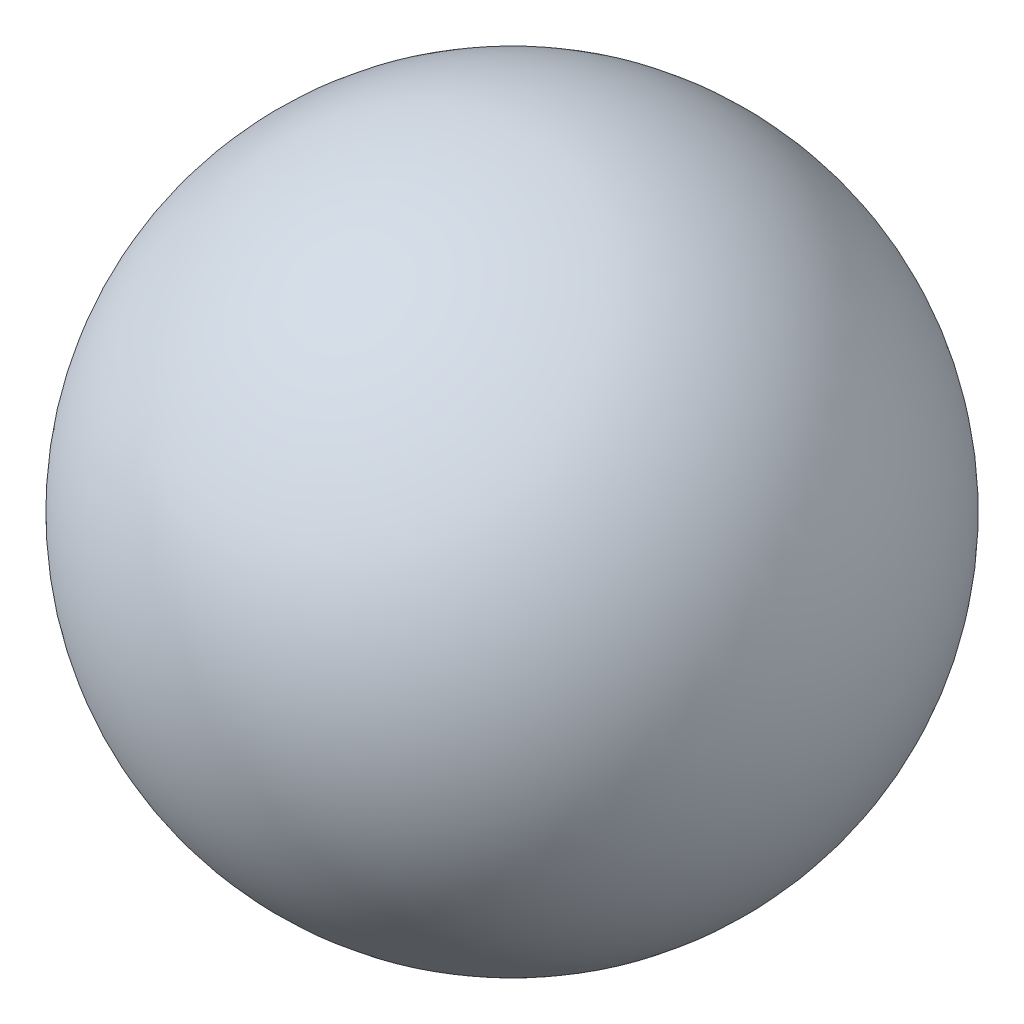
SolidWorks part; units mm, degrees
ref_plane "Plano frontal" through (0, 0, 0) normal (0, 0, 1) x (1, 0, 0)
ref_plane "Plano superior" through (0, 0, 0) normal (0, 1, 0) x (1, 0, 0)
ref_plane "Plano direito" through (0, 0, 0) normal (1, 0, 0) x (0, 0, -1)
sketch "Sketch1" plane through (0, 0, 0) normal (0, 0, 1) x (1, 0, 0)
  line L0 (0, 0) -> (0, 0.25) construction
  line L1 (0, 0.25) -> (0, 0) construction
  line L2 (0, 0) -> (0, -0.25) construction
  line L3 (0, 0.25) -> (0, -0.25)
  arc A0 (0, 0.25) -> (0, -0.25) centre (0, 0) ccw
  dimension "D1" = 0.5
revolve "Revolve1" add sketch "Sketch1" angle 360 about L3
